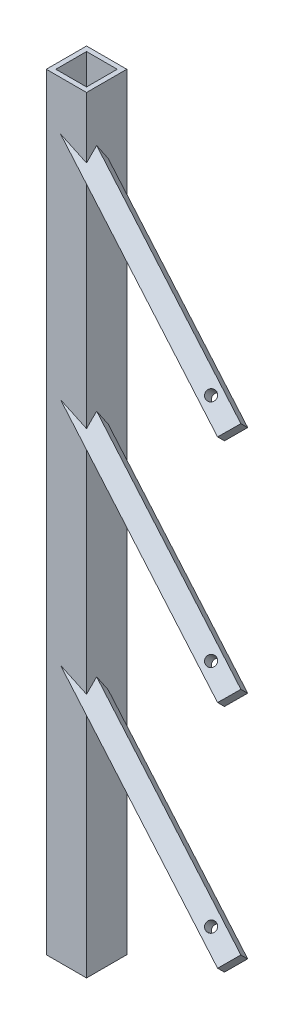
SolidWorks part; units mm, degrees
ref_plane "Front Plane" through (0, 0, 0) normal (0, 0, 1) x (1, 0, 0)
ref_plane "Top Plane" through (0, 0, 0) normal (0, 1, 0) x (1, 0, 0)
ref_plane "Right Plane" through (0, 0, 0) normal (1, 0, 0) x (0, 0, -1)
sketch "Sketch2" plane through (0, 0, 0) normal (0, 1, 0) x (1, 0, 0)
  line L1 (-10.5, 10.5) -> (10.5, 10.5)
  line L2 (-10.5, 10.5) -> (-10.5, -10.5)
  line L3 (-10.5, -10.5) -> (10.5, -10.5)
  line L4 (10.5, 10.5) -> (10.5, -10.5)
  line L5 (-10.5, 10.5) -> (10.5, -10.5) construction
  line L6 (-10.5, -10.5) -> (10.5, 10.5) construction
  point P0 (0, 0)
  dimension "D1" = 21
  dimension "D2" = 21
extrude "Boss-Extrude1" add sketch "Sketch2" along normal blind 300 and the other way blind 100
sketch "Sketch3" plane through (0, -100, 0) normal (0, -1, 0) x (1, 0, 0)
  line L1 (-8, 8) -> (8, 8)
  line L2 (-8, 8) -> (-8, -8)
  line L3 (-8, -8) -> (8, -8)
  line L4 (8, 8) -> (8, -8)
  line L5 (-8, 8) -> (8, -8) construction
  line L6 (-8, -8) -> (8, 8) construction
  point P0 (0, 0)
extrude "Cut-Extrude1" cut sketch "Sketch3" against normal blind 800
sketch "Sketch7" plane through (10.5, 0, 0) normal (1, 0, 0) x (0, 0, -1)
  line L0 (-10.5, 28.157) -> (10.5, 49.157)
  line L1 (-10.5, 300) -> (-10.5, -100) construction
  line L2 (10.5, 300) -> (10.5, -100) construction
sketch "Sketch8" plane through (0, 0, -10.5) normal (0, 0, -1) x (-1, 0, 0)
  line L0 (-10.5, 49.1574) -> (3.0946, 55.4967)
  line L1 (-10.5, 300) -> (-10.5, -100) construction
sketch "Sketch9" plane through (0, 0, 10.5) normal (0, 0, 1) x (1, 0, 0)
  line L0 (10.5, 28.157) -> (-3.0946, 34.4963)
ref_plane "Plane1" through (9.1588, 19.6412, 19.6412) normal (0.3131, 0.6715, 0.6715) x (0.9497, -0.2214, -0.2214)
sketch "Sketch14" plane through (9.1588, 19.6412, 19.6412) normal (0.3131, 0.6715, 0.6715) x (0.9497, -0.2214, -0.2214)
  line L0 (-12.9024, 16.9679) -> (98.0083, -50.8466)
  line L1 (98.0083, -50.8466) -> (103.2248, -42.3151)
  line L2 (103.2248, -42.3151) -> (-7.6859, 25.4995)
  line L3 (-7.6859, 25.4995) -> (-12.9024, 16.9679)
  circle A0 centre (87.8192, -38.7561) radius 2.5
  dimension "D3" = 5
  dimension "D4" = 5
  dimension "D5" = 15
  dimension "D1" = 130
  dimension "D2" = 10
  dimension "D6" = 130
extrude "Boss-Extrude3" add sketch "Sketch14" against normal blind 10
pattern_linear "LPattern1" count 3 spacing 120 along (0, 1, 0) of "Boss-Extrude3"
